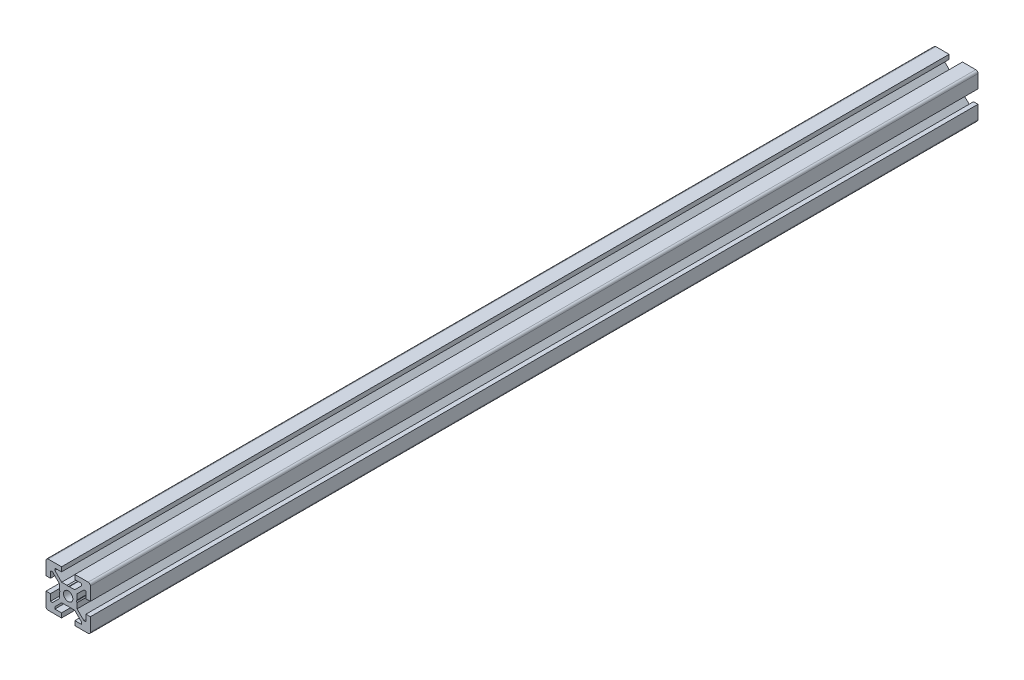
SolidWorks part; units mm, degrees
material "5052-H32"
ref_plane "Front Plane" through (0, 0, 0) normal (0, 0, 1) x (1, 0, 0)
ref_plane "Top Plane" through (0, 0, 0) normal (0, 1, 0) x (1, 0, 0)
ref_plane "Right Plane" through (0, 0, 0) normal (1, 0, 0) x (0, 0, -1)
ref_plane "Plane1" through (0, 0, -350) normal (0, 0, -1) x (-1, 0, 0)
sketch "Sketch1" plane through (0, 0, -350) normal (0, 0, -1) x (-1, 0, 0)
  line L0 (8, -3) -> (8, -6)
  line L1 (8, -6) -> (7.0607, -6)
  line L2 (7.0607, -6) -> (4, -2.9393)
  line L3 (4, -2.9393) -> (4, -0.5196)
  line L4 (4, -0.5196) -> (3.7, 0)
  line L5 (3.7, 0) -> (4, 0.5196)
  line L6 (4, 0.5196) -> (4, 2.9393)
  line L7 (4, 2.9393) -> (7.0607, 6)
  line L8 (7.0607, 6) -> (8, 6)
  line L9 (8, 6) -> (8, 3)
  line L10 (8, 3) -> (10, 3)
  line L11 (10, 3) -> (10, 9)
  line L12 (9, 10) -> (3, 10)
  line L13 (3, 10) -> (3, 8)
  line L14 (3, 8) -> (6, 8)
  line L15 (6, 8) -> (6, 7.0607)
  line L16 (6, 7.0607) -> (2.9393, 4)
  line L17 (2.9393, 4) -> (0.5196, 4)
  line L18 (0.5196, 4) -> (0, 3.7)
  line L19 (0, 3.7) -> (-0.5196, 4)
  line L20 (-0.5196, 4) -> (-2.9393, 4)
  line L21 (-2.9393, 4) -> (-6, 7.0607)
  line L22 (-6, 7.0607) -> (-6, 8)
  line L23 (-6, 8) -> (-3, 8)
  line L24 (-3, 8) -> (-3, 10)
  line L25 (-3, 10) -> (-9, 10)
  line L26 (-10, 9) -> (-10, 3)
  line L27 (-10, 3) -> (-8, 3)
  line L28 (-8, 3) -> (-8, 6)
  line L29 (-8, 6) -> (-7.0607, 6)
  line L30 (-7.0607, 6) -> (-4, 2.9393)
  line L31 (-4, 2.9393) -> (-4, 0.5196)
  line L32 (-4, 0.5196) -> (-3.7, 0)
  line L33 (-3.7, 0) -> (-4, -0.5196)
  line L34 (-4, -0.5196) -> (-4, -2.9393)
  line L35 (-4, -2.9393) -> (-7.0607, -6)
  line L36 (-7.0607, -6) -> (-8, -6)
  line L37 (-8, -6) -> (-8, -3)
  line L38 (-8, -3) -> (-10, -3)
  line L39 (-10, -3) -> (-10, -9)
  line L40 (-9, -10) -> (-3, -10)
  line L41 (-3, -10) -> (-3, -8)
  line L42 (-3, -8) -> (-6, -8)
  line L43 (-6, -8) -> (-6, -7.0607)
  line L44 (-6, -7.0607) -> (-2.9393, -4)
  line L45 (-2.9393, -4) -> (-0.5196, -4)
  line L46 (-0.5196, -4) -> (0, -3.7)
  line L47 (0, -3.7) -> (0.5196, -4)
  line L48 (0.5196, -4) -> (2.9393, -4)
  line L49 (2.9393, -4) -> (6, -7.0607)
  line L50 (6, -7.0607) -> (6, -8)
  line L51 (6, -8) -> (3, -8)
  line L52 (3, -8) -> (3, -10)
  line L53 (3, -10) -> (9, -10)
  line L54 (10, -9) -> (10, -3)
  line L55 (10, -3) -> (8, -3)
  arc A0 (10, 9) -> (9, 10) centre (9, 9) ccw
  arc A1 (-9, 10) -> (-10, 9) centre (-9, 9) ccw
  arc A2 (-10, -9) -> (-9, -10) centre (-9, -9) ccw
  arc A3 (9, -10) -> (10, -9) centre (9, -9) ccw
  circle A4 centre (0, 0) radius 2.1
extrude "Boss-Extrude1" add sketch "Sketch1" against normal blind 350
sketch "Sketch2" plane through (0, 0, -350) normal (0, 0, -1) x (-1, 0, 0)
  line L56 (10, -3) -> (8, -3)
  line L57 (8, -3) -> (8, -6)
  line L58 (8, -6) -> (7.0607, -6)
  line L59 (7.0607, -6) -> (4, -2.9393)
  line L60 (4, -2.9393) -> (4, -0.5196)
  line L61 (4, -0.5196) -> (3.7, 0)
  line L62 (3.7, 0) -> (4, 0.5196)
  line L63 (4, 0.5196) -> (4, 2.9393)
  line L64 (4, 2.9393) -> (7.0607, 6)
  line L65 (7.0607, 6) -> (8, 6)
  line L66 (8, 6) -> (8, 3)
  line L67 (8, 3) -> (10, 3)
  line L68 (10, 3) -> (10, 9)
  line L69 (9, 10) -> (3, 10)
  line L70 (3, 10) -> (3, 8)
  line L71 (3, 8) -> (6, 8)
  line L72 (6, 8) -> (6, 7.0607)
  line L73 (6, 7.0607) -> (2.9393, 4)
  line L74 (2.9393, 4) -> (0.5196, 4)
  line L75 (0.5196, 4) -> (0, 3.7)
  line L76 (0, 3.7) -> (-0.5196, 4)
  line L77 (-0.5196, 4) -> (-2.9393, 4)
  line L78 (-2.9393, 4) -> (-6, 7.0607)
  line L79 (-6, 7.0607) -> (-6, 8)
  line L80 (-6, 8) -> (-3, 8)
  line L81 (-3, 8) -> (-3, 10)
  line L82 (-3, 10) -> (-9, 10)
  line L83 (-10, 9) -> (-10, 3)
  line L84 (-10, 3) -> (-8, 3)
  line L85 (-8, 3) -> (-8, 6)
  line L86 (-8, 6) -> (-7.0607, 6)
  line L87 (-7.0607, 6) -> (-4, 2.9393)
  line L88 (-4, 2.9393) -> (-4, 0.5196)
  line L89 (-4, 0.5196) -> (-3.7, 0)
  line L90 (-3.7, 0) -> (-4, -0.5196)
  line L91 (-4, -0.5196) -> (-4, -2.9393)
  line L92 (-4, -2.9393) -> (-7.0607, -6)
  line L93 (-7.0607, -6) -> (-8, -6)
  line L94 (-8, -6) -> (-8, -3)
  line L95 (-8, -3) -> (-10, -3)
  line L96 (-10, -3) -> (-10, -9)
  line L97 (-9, -10) -> (-3, -10)
  line L98 (-3, -10) -> (-3, -8)
  line L99 (-3, -8) -> (-6, -8)
  line L100 (-6, -8) -> (-6, -7.0607)
  line L101 (-6, -7.0607) -> (-2.9393, -4)
  line L102 (-2.9393, -4) -> (-0.5196, -4)
  line L103 (-0.5196, -4) -> (0, -3.7)
  line L104 (0, -3.7) -> (0.5196, -4)
  line L105 (0.5196, -4) -> (2.9393, -4)
  line L106 (2.9393, -4) -> (6, -7.0607)
  line L107 (6, -7.0607) -> (6, -8)
  line L108 (6, -8) -> (3, -8)
  line L109 (3, -8) -> (3, -10)
  line L110 (3, -10) -> (9, -10)
  line L111 (10, -9) -> (10, -3)
  line L112 (10, -3) -> (8, -3)
  line L113 (8, -3) -> (8, -6)
  line L114 (8, -6) -> (7.0607, -6)
  line L115 (7.0607, -6) -> (4, -2.9393)
  line L116 (4, -2.9393) -> (4, -0.5196)
  line L117 (4, -0.5196) -> (3.7, 0)
  line L118 (3.7, 0) -> (4, 0.5196)
  line L119 (4, 0.5196) -> (4, 2.9393)
  line L120 (4, 2.9393) -> (7.0607, 6)
  line L121 (7.0607, 6) -> (8, 6)
  line L122 (8, 6) -> (8, 3)
  line L123 (8, 3) -> (10, 3)
  line L124 (10, 3) -> (10, 9)
  line L125 (9, 10) -> (3, 10)
  line L126 (3, 10) -> (3, 8)
  line L127 (3, 8) -> (6, 8)
  line L128 (6, 8) -> (6, 7.0607)
  line L129 (6, 7.0607) -> (2.9393, 4)
  line L130 (2.9393, 4) -> (0.5196, 4)
  line L131 (0.5196, 4) -> (0, 3.7)
  line L132 (0, 3.7) -> (-0.5196, 4)
  line L133 (-0.5196, 4) -> (-2.9393, 4)
  line L134 (-2.9393, 4) -> (-6, 7.0607)
  line L135 (-6, 7.0607) -> (-6, 8)
  line L136 (-6, 8) -> (-3, 8)
  line L137 (-3, 8) -> (-3, 10)
  line L138 (-3, 10) -> (-9, 10)
  line L139 (-10, 9) -> (-10, 3)
  line L140 (-10, 3) -> (-8, 3)
  line L141 (-8, 3) -> (-8, 6)
  line L142 (-8, 6) -> (-7.0607, 6)
  line L143 (-7.0607, 6) -> (-4, 2.9393)
  line L144 (-4, 2.9393) -> (-4, 0.5196)
  line L145 (-4, 0.5196) -> (-3.7, 0)
  line L146 (-3.7, 0) -> (-4, -0.5196)
  line L147 (-4, -0.5196) -> (-4, -2.9393)
  line L148 (-4, -2.9393) -> (-7.0607, -6)
  line L149 (-7.0607, -6) -> (-8, -6)
  line L150 (-8, -6) -> (-8, -3)
  line L151 (-8, -3) -> (-10, -3)
  line L152 (-10, -3) -> (-10, -9)
  line L153 (-9, -10) -> (-3, -10)
  line L154 (-3, -10) -> (-3, -8)
  line L155 (-3, -8) -> (-6, -8)
  line L156 (-6, -8) -> (-6, -7.0607)
  line L157 (-6, -7.0607) -> (-2.9393, -4)
  line L158 (-2.9393, -4) -> (-0.5196, -4)
  line L159 (-0.5196, -4) -> (0, -3.7)
  line L160 (0, -3.7) -> (0.5196, -4)
  line L161 (0.5196, -4) -> (2.9393, -4)
  line L162 (2.9393, -4) -> (6, -7.0607)
  line L163 (6, -7.0607) -> (6, -8)
  line L164 (6, -8) -> (3, -8)
  line L165 (3, -8) -> (3, -10)
  line L166 (3, -10) -> (9, -10)
  line L167 (10, -9) -> (10, -3)
  circle A0 centre (0, 0) radius 2.1 construction
  circle A1 centre (0, 0) radius 2.1
  arc A4 (10, 9) -> (9, 10) centre (9, 9) ccw
  arc A5 (-9, 10) -> (-10, 9) centre (-9, 9) ccw
  arc A6 (-10, -9) -> (-9, -10) centre (-9, -9) ccw
  arc A7 (9, -10) -> (10, -9) centre (9, -9) ccw
  arc A8 (10, 9) -> (9, 10) centre (9, 9) ccw
  arc A9 (-9, 10) -> (-10, 9) centre (-9, 9) ccw
  arc A10 (-10, -9) -> (-9, -10) centre (-9, -9) ccw
  arc A11 (9, -10) -> (10, -9) centre (9, -9) ccw
  dimension "D1" = 0
extrude "Boss-Extrude2" add sketch "Sketch2" along normal blind 50
